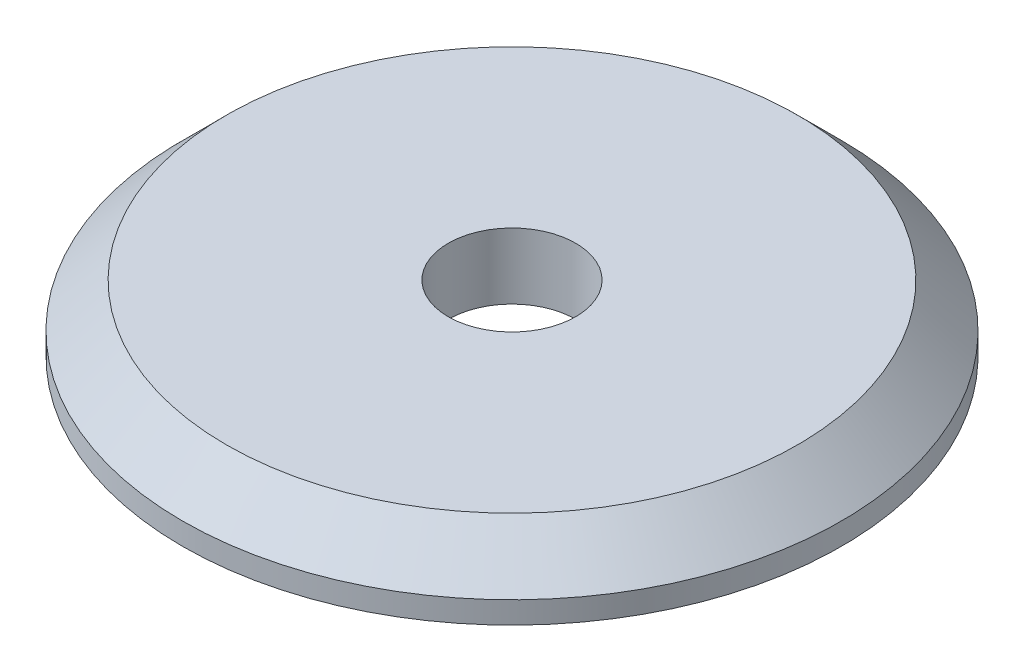
SolidWorks part; units mm, degrees
ref_plane "Front Plane" through (0, 0, 0) normal (0, 0, 1) x (1, 0, 0)
ref_plane "Top Plane" through (0, 0, 0) normal (0, 1, 0) x (1, 0, 0)
ref_plane "Right Plane" through (0, 0, 0) normal (1, 0, 0) x (0, 0, -1)
sketch "Sketch1" plane through (0, 0, 0) normal (0, 1, 0) x (1, 0, 0)
  circle A0 centre (0, 0) radius 15
  dimension "D1" = 30
extrude "Boss-Extrude1" add sketch "Sketch1" along normal blind 3
chamfer "Chamfer1" distance 2 angle 45 1 edges at (0, 3, 15)
hole_wizard "M5 Clearance Hole1" positions "Sketch2" profile "Sketch3" hole size "M5" standard "ANSI Metric"
sketch "Sketch2" plane through (0, 3, 0) normal (0, 1, 0) x (1, 0, 0)
  point P0 (0, 0)
sketch "Sketch3" plane through (0, 3, 0) normal (1, 0, 0) x (0, 0, 1)
  line L0 (0, 0) -> (0, 7.7425)
  line L1 (0, 7.7425) -> (2.9, 6)
  line L2 (2.9, 6) -> (2.9, 0)
  line L5 (2.9, 0) -> (0, 0)
  line L10 (0, 7.7425) -> (-2.9, 6) construction
  line L11 (0, -6.35) -> (0, 107.95) construction
  dimension "Hole Dia." = 5.8
  dimension "Hole Depth" = 6
  dimension "Drill Angle" = 118
